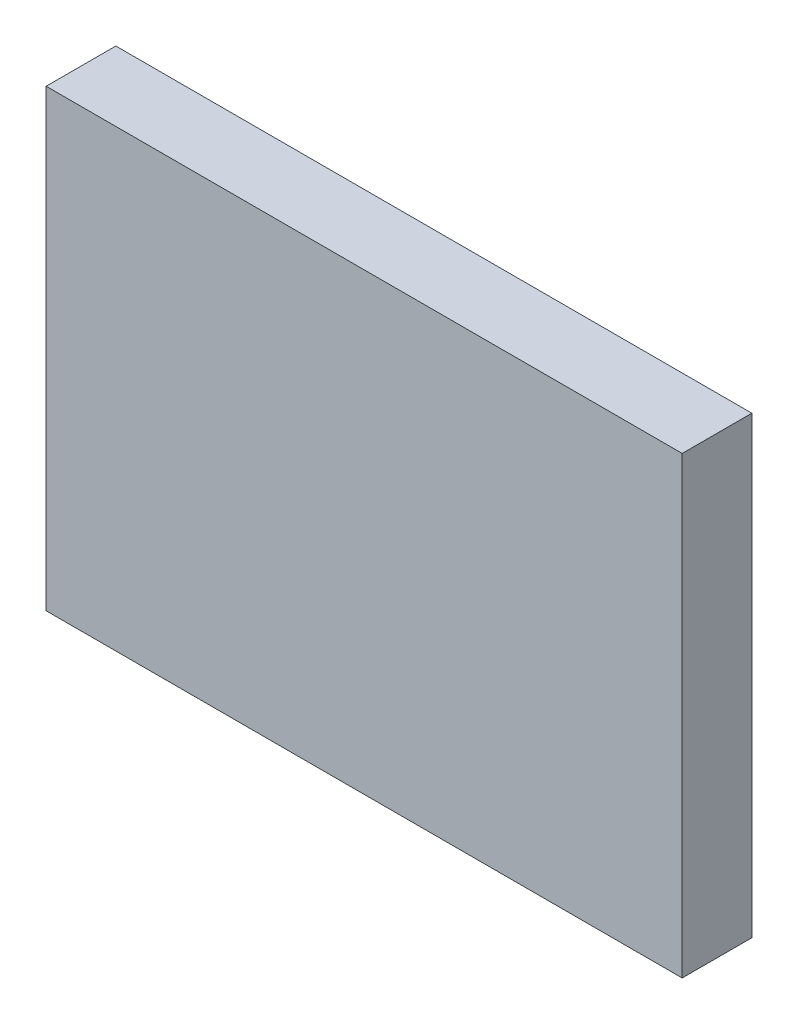
SolidWorks part; units mm, degrees
ref_plane "前视基准面" through (0, 0, 0) normal (0, 0, 1) x (1, 0, 0)
ref_plane "上视基准面" through (0, 0, 0) normal (0, 1, 0) x (1, 0, 0)
ref_plane "右视基准面" through (0, 0, 0) normal (1, 0, 0) x (0, 0, -1)
sketch "草图1" plane through (0, 0, 0) normal (0, 0, 1) x (1, 0, 0)
  line L0 (43.8075, 23.2816) -> (64.8075, 23.2816)
  line L1 (43.8075, 38.2816) -> (64.8075, 38.2816)
  line L2 (43.8075, 38.2816) -> (43.8075, 23.2816)
  line L3 (64.8075, 38.2816) -> (64.8075, 23.2816)
  dimension "D1" = 21
  dimension "D2" = 15
extrude "凸台-拉伸1" add sketch "草图1" along normal blind 2.3
